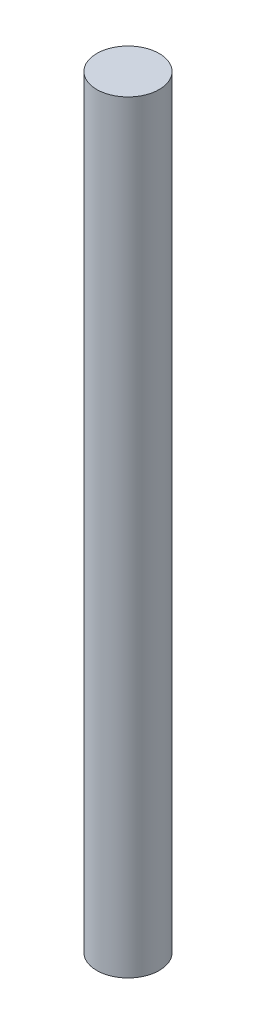
SolidWorks part; units mm, degrees
ref_plane "Front Plane" through (0, 0, 0) normal (0, 0, 1) x (1, 0, 0)
ref_plane "Top Plane" through (0, 0, 0) normal (0, 1, 0) x (1, 0, 0)
ref_plane "Right Plane" through (0, 0, 0) normal (1, 0, 0) x (0, 0, -1)
sketch "Sketch1" plane through (0, 0, 0) normal (0, 1, 0) x (1, 0, 0)
  circle A0 centre (0, 0) radius 2.25
  dimension "D1" = 4.5
extrude "Boss-Extrude1" add sketch "Sketch1" along normal blind 55
